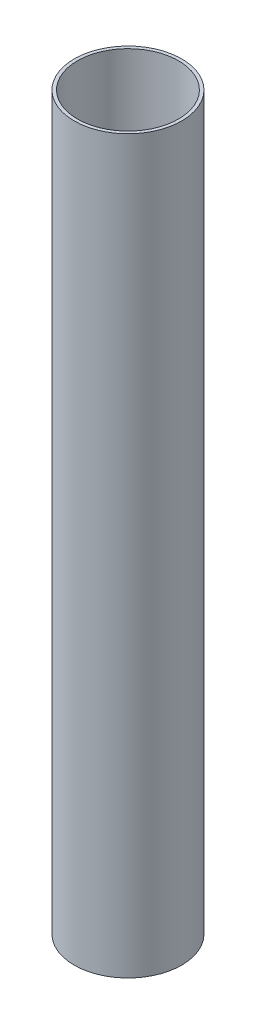
SolidWorks part; units mm, degrees
material "6063-T6"
ref_plane "Front Plane" through (0, 0, 0) normal (0, 0, 1) x (1, 0, 0)
ref_plane "Top Plane" through (0, 0, 0) normal (0, 1, 0) x (1, 0, 0)
ref_plane "Right Plane" through (0, 0, 0) normal (1, 0, 0) x (0, 0, -1)
sketch "Sketch1" plane through (0, 0, 0) normal (0, 1, 0) x (1, 0, 0)
  circle A0 centre (0, 0) radius 50
  circle A1 centre (0, 0) radius 47
  dimension "D1" = 100
  dimension "D2" = 3
extrude "Boss-Extrude1" add sketch "Sketch1" along normal blind 680
